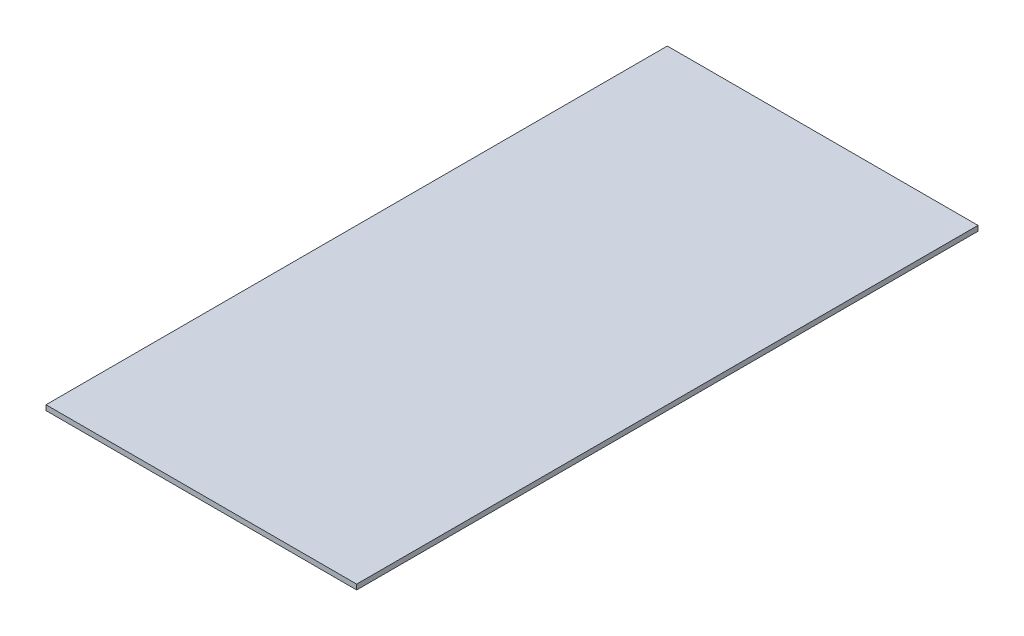
SolidWorks part; units mm, degrees
ref_plane "Front Plane" through (0, 0, 0) normal (0, 0, 1) x (1, 0, 0)
ref_plane "Top Plane" through (0, 0, 0) normal (0, 1, 0) x (1, 0, 0)
ref_plane "Right Plane" through (0, 0, 0) normal (1, 0, 0) x (0, 0, -1)
sketch "Sketch1" plane through (0, 0, 0) normal (0, 1, 0) x (1, 0, 0)
  line L1 (-582.0302, 629.001) -> (27.5698, 629.001)
  line L2 (-582.0302, 629.001) -> (-582.0302, -590.199)
  line L3 (-582.0302, -590.199) -> (27.5698, -590.199)
  line L4 (27.5698, 629.001) -> (27.5698, -590.199)
  dimension "D1" = 1219.2
  dimension "D2" = 609.6
extrude "Boss-Extrude1" add sketch "Sketch1" along normal blind 10
sketch "Sketch2" plane through (0, 10, 0) normal (0, 1, 0) x (1, 0, 0)
  line L0 (1411.6289, 1403.7379) -> (1136.424, -194.0016) construction
